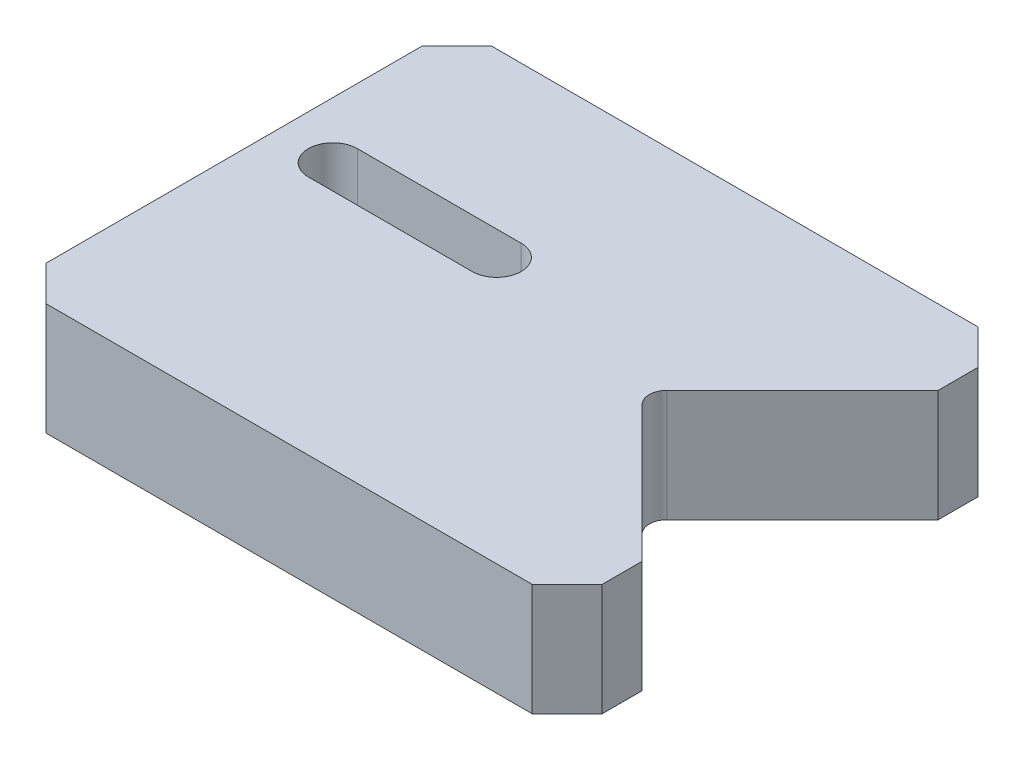
SolidWorks part; units mm, degrees
ref_plane "Plano frontal" through (0, 0, 0) normal (0, 0, 1) x (1, 0, 0)
ref_plane "Plano superior" through (0, 0, 0) normal (0, 1, 0) x (1, 0, 0)
ref_plane "Plano direito" through (0, 0, 0) normal (1, 0, 0) x (0, 0, -1)
sketch "Esboço1" plane through (0, 0, 0) normal (0, 1, 0) x (1, 0, 0)
  line L0 (-31.75, 0) -> (14.85, 0) construction
  line L1 (-27.75, 25.45) -> (27.75, 25.45)
  line L2 (-31.75, 21.45) -> (-31.75, -21.45)
  line L3 (-27.75, -25.45) -> (27.75, -25.45)
  line L4 (31.75, 21.45) -> (31.75, 16.9)
  line L5 (-4.2168, 3.3801) -> (31.75, -25.45) construction
  line L6 (-31.75, -25.45) -> (31.75, 25.45) construction
  line L7 (16.2642, 1.4142) -> (31.75, 16.9)
  line L8 (16.2642, -1.4142) -> (31.75, -16.9)
  line L10 (31.75, -16.9) -> (31.75, -21.45)
  line L11 (27.75, 25.45) -> (31.75, 21.45)
  line L12 (27.75, -25.45) -> (31.75, -21.45)
  line L13 (-31.75, 21.45) -> (-27.75, 25.45)
  line L14 (-31.75, -21.45) -> (-27.75, -25.45)
  line L15 (-25.3, 7.65) -> (-6.6, 7.65)
  line L16 (-25.3, 2.05) -> (-6.6, 2.05)
  arc A0 (16.2642, -1.4142) -> (16.2642, 1.4142) centre (17.6784, 0) cw
  arc A1 (-25.3, 7.65) -> (-25.3, 2.05) centre (-25.3, 4.85) ccw
  arc A2 (-6.6, 2.05) -> (-6.6, 7.65) centre (-6.6, 4.85) ccw
  point P0 (0, 0)
  dimension "D3" = 2
  dimension "D4" = 6.45
  dimension "D7" = 18.7
  dimension "D1" = 63.5
  dimension "D2" = 50.9
  dimension "D8" = 20.6
extrude "Ressalto-extrusão2" add sketch "Esboço1" along normal blind 12.8
